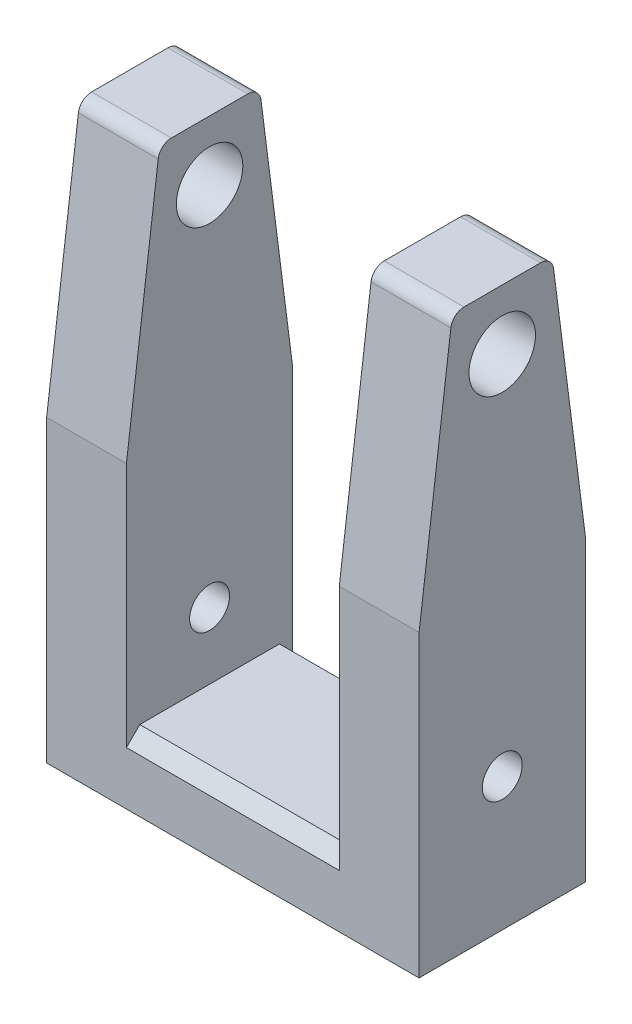
SolidWorks part; units mm, degrees
ref_plane "Front Plane" through (0, 0, 0) normal (0, 0, 1) x (1, 0, 0)
ref_plane "Top Plane" through (0, 0, 0) normal (0, 1, 0) x (1, 0, 0)
ref_plane "Right Plane" through (0, 0, 0) normal (1, 0, 0) x (0, 0, -1)
sketch "Sketch1" plane through (0, 0, 0) normal (1, 0, 0) x (0, 0, -1)
  line L0 (-12.5, 45) -> (-7.7238, 82.2543)
  line L2 (12.5, 45) -> (12.5, 0)
  line L3 (12.5, 0) -> (-12.5, 0)
  line L4 (-12.5, 45) -> (-12.5, 0)
  line L7 (-5.74, 84) -> (5.74, 84)
  line L8 (7.7238, 82.2543) -> (12.5, 45)
  circle A0 centre (0, 20) radius 3
  circle A1 centre (0, 75) radius 5
  arc A2 (5.74, 84) -> (7.7238, 82.2543) centre (5.74, 82) cw
  arc A3 (-7.7238, 82.2543) -> (-5.74, 84) centre (-5.74, 82) cw
  point P11 (0, 0)
  point P13 (7.5, 84)
  point P16 (-7.5, 84)
  point P17 (0, 84)
  point P19 (0, 0)
  dimension "D6" = 6
  dimension "D7" = 10
  dimension "D8" = 2
  dimension "D1" = 25
  dimension "D2" = 45
  dimension "D3" = 84
  dimension "D4" = 75
  dimension "D5" = 15
  dimension "D9" = 45
  dimension "D10" = 20
extrude "Boss-Extrude1" add sketch "Sketch1" along normal blind 12
sketch "Sketch3" plane through (0, 0, 0) normal (-1, 0, 0) x (0, 0, 1)
  line L1 (12.5, 10) -> (-12.5, 10)
  line L2 (12.5, 10) -> (12.5, 0)
  line L3 (12.5, 0) -> (-12.5, 0)
  line L4 (-12.5, 10) -> (-12.5, 0)
  line L5 (12.5, 10) -> (-12.5, 0) construction
  line L6 (12.5, 0) -> (-12.5, 10) construction
  point P0 (0, 5)
  dimension "D1" = 10
extrude "Boss-Extrude2" add sketch "Sketch3" along normal blind 16
mirror "Mirror2" about plane through (-16, 0, 0) normal (1, 0, 0) of bodies 102
chamfer "Chamfer1" distance 2 angle 45 2 edges at (-16, 10, 12.5) (-16, 10, -12.5)
